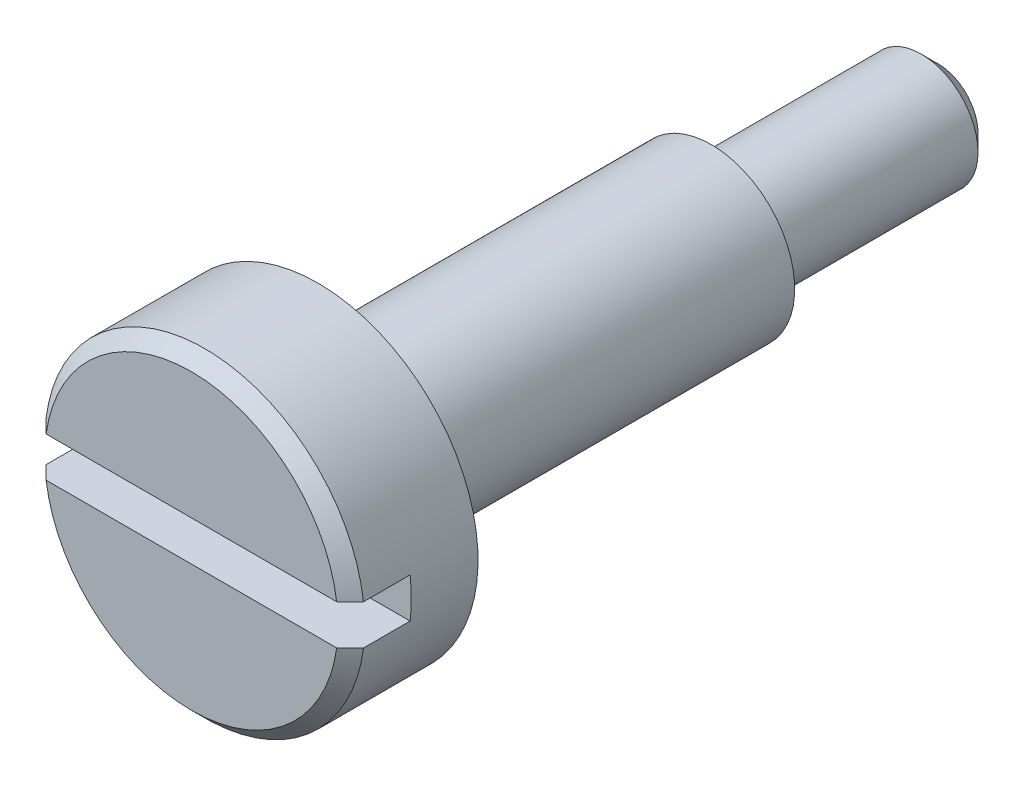
SolidWorks part; units mm, degrees
ref_plane "Front Plane" through (0, 0, 0) normal (0, 0, 1) x (1, 0, 0)
ref_plane "Top Plane" through (0, 0, 0) normal (0, 1, 0) x (1, 0, 0)
ref_plane "Right Plane" through (0, 0, 0) normal (1, 0, 0) x (0, 0, -1)
sketch "Sketch2" plane through (0, 0, 0) normal (0, 0, 1) x (1, 0, 0)
  circle A0 centre (0, 0) radius 2.4
  dimension "D1" = 4.8
extrude "Boss-Extrude1" add sketch "Sketch2" against normal blind 11.2 contours A0
sketch "Sketch4" plane through (0, 0, -11.2) normal (0, 0, -1) x (-1, 0, 0)
  circle A0 centre (0, 0) radius 1.25
  dimension "D1" = 2.5
extrude "Cut-Extrude1" cut sketch "Sketch4" against normal blind 9.3 flip side to cut
sketch "Sketch5" plane through (0, 0, -11.2) normal (0, 0, -1) x (-1, 0, 0)
  circle A0 centre (0, 0) radius 0.85
  dimension "D1" = 1.7
extrude "Cut-Extrude2" cut sketch "Sketch5" against normal blind 3.4 flip side to cut
cosmetic thread "Cosmetic Thread1" parameters "D1"=1.6, "D2"=1.302
sketch "Sketch6" plane through (0, 0, 0) normal (0, 0, 1) x (1, 0, 0)
  line L1 (-2.5, -0.3) -> (2.5, -0.3)
  line L2 (-2.5, -0.3) -> (-2.5, 0.3)
  line L3 (-2.5, 0.3) -> (2.5, 0.3)
  line L4 (2.5, -0.3) -> (2.5, 0.3)
  line L5 (-2.5, -0.3) -> (2.5, 0.3) construction
  line L6 (-2.5, 0.3) -> (2.5, -0.3) construction
  circle A3 centre (0, 0) radius 2.4 construction
  point P0 (0, 0)
  dimension "D1" = 0.6
  dimension "D2" = 0.1
extrude "Cut-Extrude3" cut sketch "Sketch6" against normal blind 0.9 contours L3 L4 L1 L2
fillet "Fillet1" radius 0.1 2 edges at (-1.25, 0, -1.9) (-0.85, 0, -7.8)
chamfer "Chamfer2" distance 0.2 angle 45 2 edges at (0, -2.4, 0) (0, 2.4, 0)
chamfer "Chamfer1" distance 0.25 angle 45 1 edges at (-0.85, 0, -11.2)
